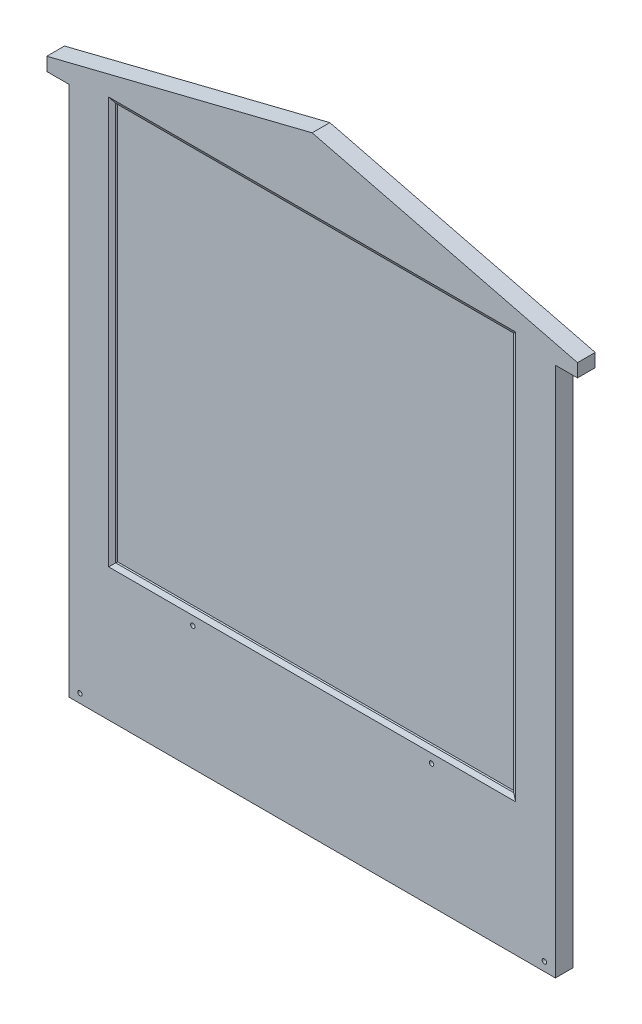
SolidWorks part; units mm, degrees
ref_plane "Front" through (0, 0, 0) normal (0, 0, 1) x (1, 0, 0)
ref_plane "Top" through (0, 0, 0) normal (0, 1, 0) x (1, 0, 0)
ref_plane "Right" through (0, 0, 0) normal (1, 0, 0) x (0, 0, -1)
sketch "草图1" plane through (0, 0, 0) normal (0, 1, 0) x (1, 0, 0)
  line L1 (55, -2) -> (-55, -2)
  line L2 (55, -2) -> (55, 2)
  line L3 (55, 2) -> (-55, 2)
  line L4 (-55, -2) -> (-55, 2)
  line L5 (55, -2) -> (-55, 2) construction
  line L6 (55, 2) -> (-55, -2) construction
  point P0 (0, 0)
  dimension "D1" = 110
  dimension "D2" = 4
extrude "凸台-拉伸1" add sketch "草图1" along normal blind 120
sketch "草图2" plane through (0, 120, 0) normal (0, 1, 0) x (1, 0, 0)
  line L0 (55, 2) -> (-55, 2) construction
  line L1 (60, -2) -> (-60, -2)
  line L2 (60, -2) -> (60, 2)
  line L3 (60, 2) -> (-60, 2)
  line L4 (-60, -2) -> (-60, 2)
  line L5 (60, -2) -> (-60, 2) construction
  line L6 (60, 2) -> (-60, -2) construction
  point P0 (0, 0)
  dimension "D1" = 120
extrude "凸台-拉伸2" add sketch "草图2" along normal blind 18
sketch "草图3" plane through (0, 0, 2) normal (0, 0, 1) x (1, 0, 0)
  line L0 (0, 0) -> (0, 190.2007) construction
  line L1 (-55, 0) -> (55, 0) construction
  line L2 (-60, 138) -> (0, 138)
  line L3 (-60, 138) -> (60, 138) construction
  line L4 (0, 138) -> (-60, 123)
  line L5 (-60, 123) -> (-60, 138)
  line L6 (-60, 138) -> (-60, 120) construction
  line L7 (-60, 120) -> (-55, 120) construction
  point P11 (-60, 130)
  point P12 (-60, 133.3477)
  dimension "D1" = 3
extrude "切除-拉伸1" cut sketch "草图3" against normal through all
ref_plane "基准面1" through (0, 0, 0) normal (1, 0, 0) x (0, 0, -1)
mirror "镜向1" about plane through (0, 0, 0) normal (1, 0, 0) of "切除-拉伸1"
sketch "草图4" plane through (0, 0, 2) normal (0, 0, 1) x (1, 0, 0)
  line L0 (0, -55) -> (0, 55) construction
  line L1 (45, 31) -> (-45, 31)
  line L2 (45, 31) -> (45, 121)
  line L3 (45, 121) -> (-45, 121)
  line L4 (-45, 31) -> (-45, 121)
  line L5 (45, 31) -> (-45, 121) construction
  line L6 (45, 121) -> (-45, 31) construction
  point P0 (0, 76)
  point P5 (0, 0)
  dimension "D1" = 90
  dimension "D2" = 90
  dimension "D3" = 17
extrude "切除-拉伸2" cut sketch "草图4" against normal blind 1
sketch "草图6" plane through (0, 0, -2) normal (0, 0, -1) x (-1, 0, 0)
  line L0 (0, 55) -> (0, -55) construction
  line L1 (-55, 0) -> (55, 0) construction
  circle A0 centre (-52.5, 2) radius 0.5
  circle A1 centre (-27, 28) radius 0.5
  circle A2 centre (27, 28) radius 0.5
  circle A3 centre (52.5, 2) radius 0.5
  dimension "D1" = 1
  dimension "D2" = 1
  dimension "D3" = 54
  dimension "D4" = 26
  dimension "D5" = 2
  dimension "D6" = 105
extrude "切除-拉伸3" cut sketch "草图6" against normal through all
sketch "草图7" plane through (0, 0, -2) normal (0, 0, -1) x (-1, 0, 0)
  circle A0 centre (-52.5, 2) radius 1.25
  circle A1 centre (-27, 28) radius 1.25
  circle A2 centre (27, 28) radius 1.25
  circle A3 centre (52.5, 2) radius 1.25
  circle A4 centre (-27, 28) radius 0.5 construction
  circle A5 centre (27, 28) radius 0.5 construction
  circle A6 centre (52.5, 2) radius 0.5 construction
  point P13 (0, 0)
  dimension "D1" = 2.5
extrude "切除-拉伸4" cut sketch "草图7" against normal blind 1
chamfer "倒角1" distance 1 angle 30 4 edges at (0, 31, 2) (45, 76, 2) (-45, 76, 2) (0, 121, 2)
